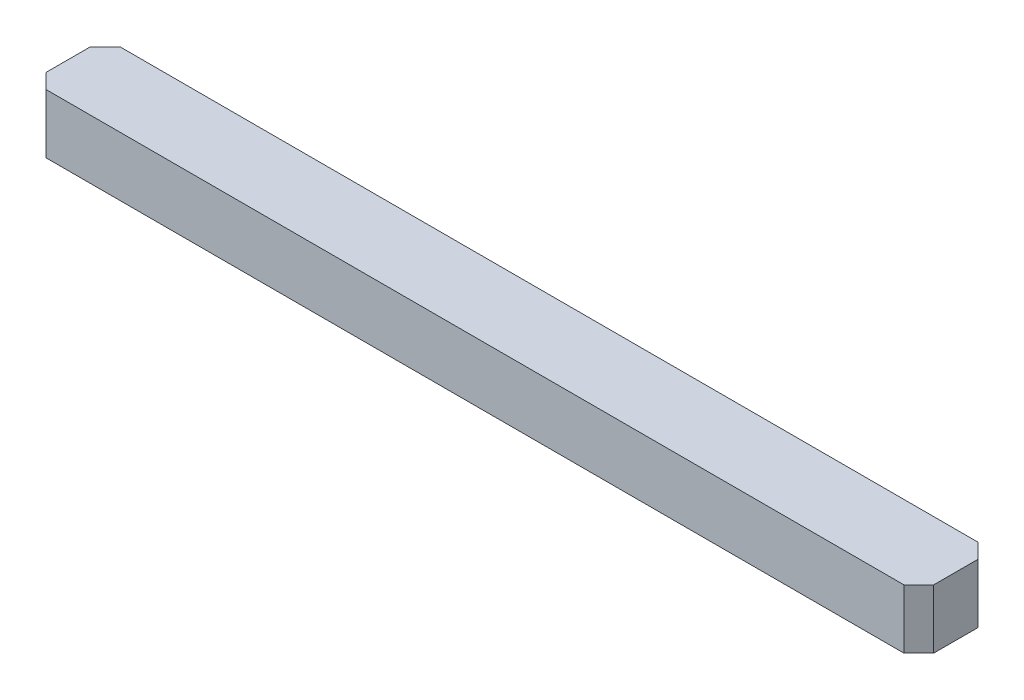
SolidWorks part; units mm, degrees
ref_plane "Front Plane" through (0, 0, 0) normal (0, 0, 1) x (1, 0, 0)
ref_plane "Top Plane" through (0, 0, 0) normal (0, 1, 0) x (1, 0, 0)
ref_plane "Right Plane" through (0, 0, 0) normal (1, 0, 0) x (0, 0, -1)
sketch "Sketch1" plane through (0, 0, 0) normal (0, 1, 0) x (1, 0, 0)
  line L1 (0, 0) -> (60, 0)
  line L2 (0, 0) -> (0, 5)
  line L3 (0, 5) -> (60, 5)
  line L4 (60, 0) -> (60, 5)
  dimension "D1" = 5
  dimension "D2" = 60
extrude "Boss-Extrude1" add sketch "Sketch1" along normal blind 4
chamfer "Chamfer1" distance 1 angle 45 4 edges at (0, 2, -5) (60, 2, -5) (60, 2, 0) (0, 2, 0)
